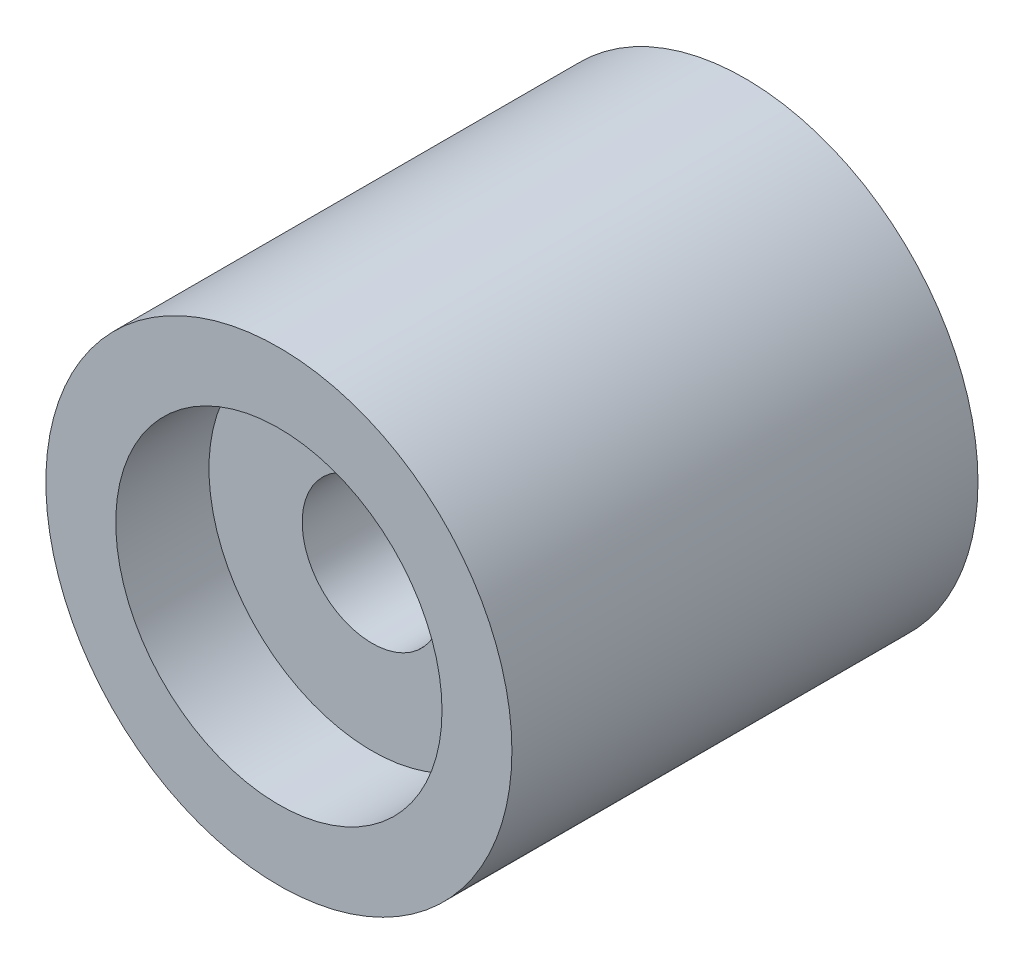
SolidWorks part; units mm, degrees
ref_plane "Front Plane" through (0, 0, 0) normal (0, 0, 1) x (1, 0, 0)
ref_plane "Top Plane" through (0, 0, 0) normal (0, 1, 0) x (1, 0, 0)
ref_plane "Right Plane" through (0, 0, 0) normal (1, 0, 0) x (0, 0, -1)
sketch "Sketch1" plane through (0, 0, 0) normal (0, 0, 1) x (1, 0, 0)
  circle A0 centre (0, 0) radius 5
  dimension "D1" = 10
extrude "Boss-Extrude1" add sketch "Sketch1" along normal blind 10
sketch "Sketch2" plane through (0, 0, 0) normal (0, 0, 1) x (1, 0, 0)
  circle A0 centre (0, 0) radius 3.5
  dimension "D1" = 7
extrude "Cut-Extrude1" cut sketch "Sketch2" along normal blind 2 contours A0
ref_plane "Plane1" through (0, 0, 10) normal (0, 0, 1) x (1, 0, 0)
sketch "Sketch3" plane through (0, 0, 10) normal (0, 0, 1) x (1, 0, 0)
  circle A0 centre (0, 0) radius 3.5
  dimension "D1" = 7
extrude "Cut-Extrude2" cut sketch "Sketch3" against normal blind 2
sketch "Sketch4" plane through (0, 0, 10) normal (0, 0, 1) x (1, 0, 0)
  circle A0 centre (0, 0) radius 1.5
  dimension "D1" = 3
extrude "Cut-Extrude3" cut sketch "Sketch4" against normal blind 12
